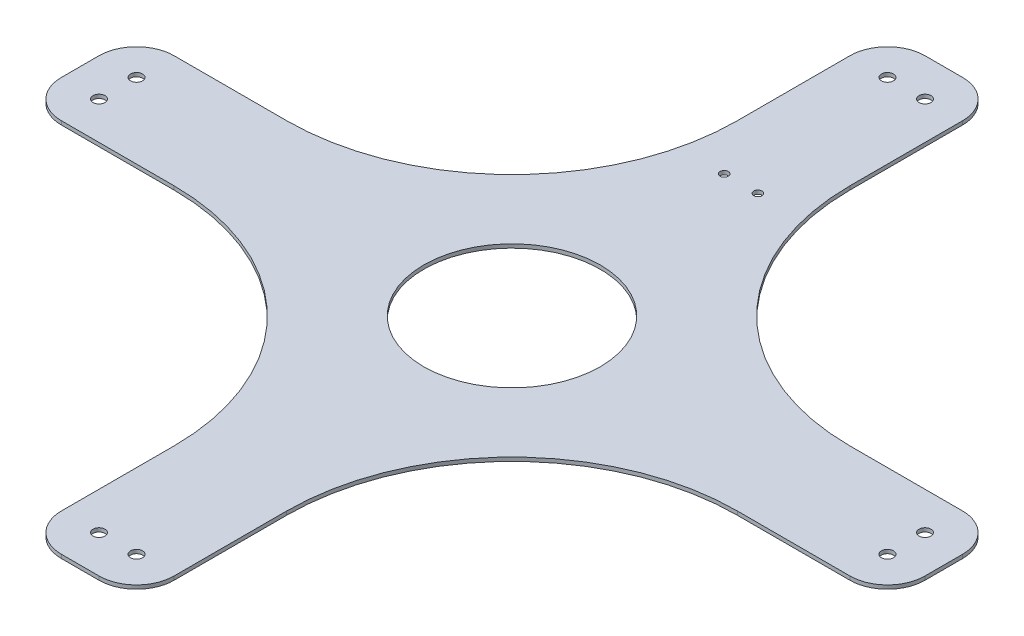
SolidWorks part; units mm, degrees
material "Thornel VCB-20 Carbon Cloth"
ref_plane "Front Plane" through (0, 0, 0) normal (0, 0, 1) x (1, 0, 0)
ref_plane "Top Plane" through (0, 0, 0) normal (0, 1, 0) x (1, 0, 0)
ref_plane "Right Plane" through (0, 0, 0) normal (1, 0, 0) x (0, 0, -1)
sketch "Sketch1" plane through (0, 0, 0) normal (0, 1, 0) x (1, 0, 0)
  line L0 (0, 115) -> (0, -115) construction
  line L1 (-115, 0) -> (115, 0) construction
  line L2 (75, 15) -> (105, 15)
  line L3 (5, 115) -> (-5, 115)
  line L4 (15, 105) -> (15, 75)
  line L5 (5, -115) -> (-5, -115)
  line L6 (-15, 105) -> (-15, 75)
  line L7 (-105, 15) -> (-75, 15)
  line L8 (-115, 5) -> (-115, -5)
  line L9 (-105, -15) -> (-75, -15)
  line L10 (115, 5) -> (115, -5)
  line L11 (15, -75) -> (15, -105)
  line L12 (75, -15) -> (105, -15)
  line L13 (-15, -75) -> (-15, -105)
  arc A0 (5, 115) -> (15, 105) centre (5, 105) cw
  arc A1 (-5, 115) -> (-15, 105) centre (-5, 105) ccw
  arc A2 (105, 15) -> (115, 5) centre (105, 5) cw
  arc A3 (105, -15) -> (115, -5) centre (105, -5) ccw
  arc A4 (15, -105) -> (5, -115) centre (5, -105) cw
  arc A5 (-5, -115) -> (-15, -105) centre (-5, -105) cw
  arc A6 (-115, -5) -> (-105, -15) centre (-105, -5) ccw
  arc A7 (-105, 15) -> (-115, 5) centre (-105, 5) ccw
  arc A8 (75, 15) -> (15, 75) centre (75, 75) cw
  arc A9 (15, -75) -> (75, -15) centre (75, -75) cw
  arc A10 (-75, -15) -> (-15, -75) centre (-75, -75) cw
  arc A11 (-15, 75) -> (-75, 15) centre (-75, 75) cw
  point P5 (0, 0)
  point P8 (0, 0)
  point P16 (0, 115)
  point P23 (15, 115)
  point P26 (-15, 115)
  point P43 (15, -15)
  point P46 (-15, -15)
  dimension "D1" = 30
  dimension "D3" = 10
  dimension "D4" = 60
  dimension "D2" = 230
extrude "Boss-Extrude1" add sketch "Sketch1" along normal mid plane 1
hole_wizard "M3 Clearance Hole1" positions "Sketch3" profile "Sketch4" hole size "M3" standard "ANSI Metric" end condition up to next
sketch "Sketch3" plane through (0, 0.5, 0) normal (0, 1, 0) x (1, 0, 0)
  point P0 (-105, 5)
  point P3 (-105, -5)
  point P6 (-5, 105)
  point P9 (5, 105)
  point P12 (105, 5)
  point P15 (105, -5)
  point P18 (5, -105)
  point P21 (-5, -105)
sketch "Sketch4" plane through (-105, 0.5, -5) normal (1, 0, 0) x (0, 0, 1)
  line L0 (0, 0) -> (0, 1)
  line L1 (0, 1) -> (1.6, 1)
  line L2 (1.6, 1) -> (1.6, 0)
  line L5 (1.6, 0) -> (0, 0)
  line L11 (0, -6.35) -> (0, 107.95) construction
  dimension "Thru Hole Dia." = 3.2
  dimension "Thru Hole Depth" = 1
sketch "Sketch5" plane through (0, 0.5, 0) normal (0, 1, 0) x (1, 0, 0)
  circle A0 centre (0, 0) radius 23.5
  dimension "D1" = 47
extrude "Cut-Extrude1" cut sketch "Sketch5" against normal through all both and the other way through all
hole_wizard "M2 Clearance Hole1" positions "Sketch8" profile "Sketch9" hole size "M2" standard "ANSI Metric" end condition up to next
sketch "Sketch8" plane through (0, 0.5, 0) normal (0, 1, 0) x (1, 0, 0)
  line L0 (-4.5, 61) -> (4.5, 61) construction
  line L2 (0, 61) -> (0, 0) construction
  point P0 (-4.5, 61)
  point P2 (4.5, 61)
  dimension "D1" = 9
  dimension "D2" = 61
sketch "Sketch9" plane through (-4.5, 0.5, -61) normal (1, 0, 0) x (0, 0, 1)
  line L0 (0, 0) -> (0, 1)
  line L1 (0, 1) -> (1.1, 1)
  line L2 (1.1, 1) -> (1.1, 0)
  line L5 (1.1, 0) -> (0, 0)
  line L11 (0, -6.35) -> (0, 107.95) construction
  dimension "Thru Hole Dia." = 2.2
  dimension "Thru Hole Depth" = 1
